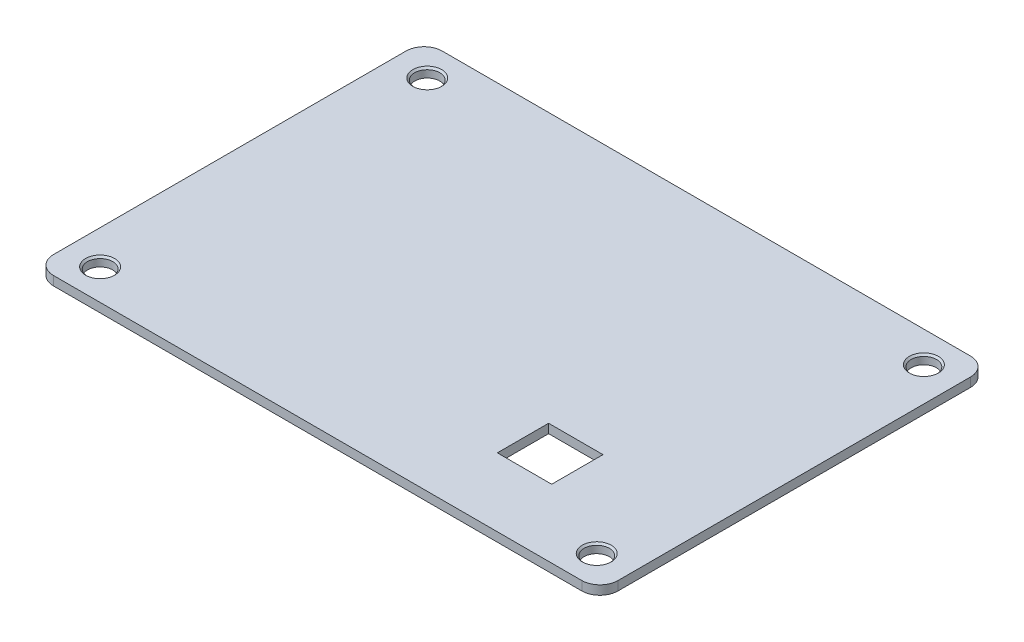
SolidWorks part; units mm, degrees
ref_plane "Płaszczyzna przednia" through (0, 0, 0) normal (0, 0, 1) x (1, 0, 0)
ref_plane "Płaszczyzna górna" through (0, 0, 0) normal (0, 1, 0) x (1, 0, 0)
ref_plane "Płaszczyzna prawa" through (0, 0, 0) normal (1, 0, 0) x (0, 0, -1)
sketch "Szkic1" plane through (0, 0, 0) normal (0, 1, 0) x (1, 0, 0)
  line L1 (-31.15, -21.45) -> (31.15, -21.45)
  line L2 (-31.15, -21.45) -> (-31.15, 21.45)
  line L3 (-31.15, 21.45) -> (31.15, 21.45)
  line L4 (31.15, -21.45) -> (31.15, 21.45)
  line L5 (-31.15, -21.45) -> (31.15, 21.45) construction
  line L6 (-31.15, 21.45) -> (31.15, -21.45) construction
  point P0 (0, 0)
  dimension "D1" = 62.3
  dimension "D2" = 42.9
extrude "Dodanie-wyciągnięcie1" add sketch "Szkic1" along normal blind 1
sketch "Szkic5" plane through (0, 1, 0) normal (0, 1, 0) x (1, 0, 0)
  line L1 (23.5, -15.5) -> (-23.5, -15.5)
  line L2 (23.5, -15.5) -> (23.5, 15.5)
  line L3 (23.5, 15.5) -> (-23.5, 15.5)
  line L4 (-23.5, -15.5) -> (-23.5, 15.5)
  line L5 (23.5, -15.5) -> (-23.5, 15.5) construction
  line L6 (23.5, 15.5) -> (-23.5, -15.5) construction
  line L7 (12.29, -13.91) -> (18.29, -13.91)
  line L8 (12.29, -13.91) -> (12.29, -8.25)
  line L9 (12.29, -8.25) -> (18.29, -8.25)
  line L10 (18.29, -13.91) -> (18.29, -8.25)
  line L11 (12.29, -13.91) -> (18.29, -8.25) construction
  line L12 (12.29, -8.25) -> (18.29, -13.91) construction
  point P0 (0, 0)
  point P6 (15.29, -11.08)
  dimension "D1" = 47
  dimension "D2" = 31
  dimension "D3" = 8.21
  dimension "D4" = 4.42
  dimension "D5" = 6
  dimension "D6" = 5.66
extrude "Wytnij-wyciągnięcie2" cut sketch "Szkic5" against normal blind 7 contours L8 L9 L10 L7
sketch "Szkic6" plane through (0, 1, 0) normal (0, 1, 0) x (1, 0, 0)
  line L0 (0, 21.45) -> (0, -21.45) construction
  line L1 (-31.15, 21.45) -> (-23.65, 21.45)
  line L2 (-31.15, 21.45) -> (-31.15, 14.65)
  line L3 (-31.15, 14.65) -> (-23.65, 14.65)
  line L4 (-23.65, 21.45) -> (-23.65, 14.65)
  line L5 (31.15, 21.45) -> (-31.15, 21.45) construction
  line L6 (-31.15, -21.45) -> (31.15, -21.45) construction
  line L7 (-31.15, 0) -> (31.15, 0) construction
  line L8 (-31.15, 21.45) -> (-31.15, -21.45) construction
  line L9 (31.15, -21.45) -> (31.15, 21.45) construction
  line L10 (-31.15, 21.45) -> (-23.65, 14.65) construction
  circle A0 centre (-27.4, 18.05) radius 1.4
  circle A1 centre (27.4, 18.05) radius 1.4
  circle A2 centre (27.4, -18.05) radius 1.4
  circle A3 centre (-27.4, -18.05) radius 1.4
  dimension "D3" = 2.8
  dimension "D1" = 7.5
  dimension "D2" = 6.8
extrude "Wytnij-wyciągnięcie3" cut sketch "Szkic6" against normal blind 10 contours A1 | A2 | A3 | A0
fillet "Zaokrąglenie1" radius 2 4 edges at (-31.15, 0.5, 21.45) (31.15, 0.5, 21.45) (31.15, 0.5, -21.45) (-31.15, 0.5, -21.45)
chamfer "Sfazowanie1" distance 0.2 angle 45 4 edges at (27.4, 1, -16.65) (27.4, 1, 19.45) (-27.4, 1, 19.45) (-27.4, 1, -16.65)
sketch "Szkic7" plane through (0, 1, 0) normal (0, 1, 0) x (1, 0, 0)
  line L2 (21.2669, -15) -> (1.2669, -15)
  line L3 (21.2669, -15) -> (21.2669, 15)
  line L4 (21.2669, 15) -> (1.2669, 15)
  line L5 (1.2669, -15) -> (1.2669, 15)
  line L7 (21.2669, 15) -> (1.2669, -15) construction
  line L10 (24.2669, -18) -> (-1.7331, -18)
  line L11 (24.2669, -18) -> (24.2669, 18)
  line L12 (24.2669, 18) -> (-1.7331, 18)
  line L13 (-1.7331, -18) -> (-1.7331, 18)
  line L14 (24.2669, -18) -> (-1.7331, 18) construction
  line L15 (24.2669, 18) -> (-1.7331, -18) construction
  point P0 (11.2669, 0)
  point P1 (11.2669, 0)
  dimension "D1" = 20
  dimension "D2" = 30
  dimension "D3" = 3
  dimension "D4" = 3
extrude "Dodanie-wyciągnięcie2" [suppressed] add sketch "Szkic7" along normal blind 10
